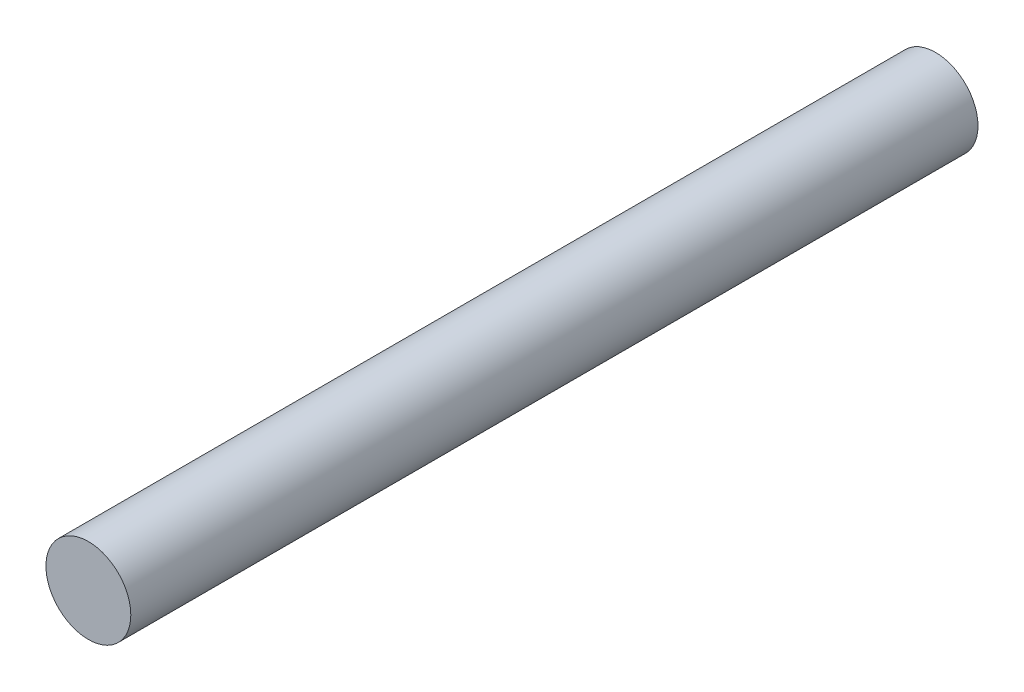
SolidWorks part; units mm, degrees
ref_plane "Front Plane" through (0, 0, 0) normal (0, 0, 1) x (1, 0, 0)
ref_plane "Top Plane" through (0, 0, 0) normal (0, 1, 0) x (1, 0, 0)
ref_plane "Right Plane" through (0, 0, 0) normal (1, 0, 0) x (0, 0, -1)
sketch "Sketch1" plane through (0, 0, 0) normal (0, 0, 1) x (1, 0, 0)
  circle A0 centre (0, 0) radius 2.475
  dimension "D1" = 4.95
extrude "Boss-Extrude1" add sketch "Sketch1" along normal blind 50.45
chamfer "Chamfer1" distance 1.5 angle 35 1 edges at (2.475, 0, 0)
